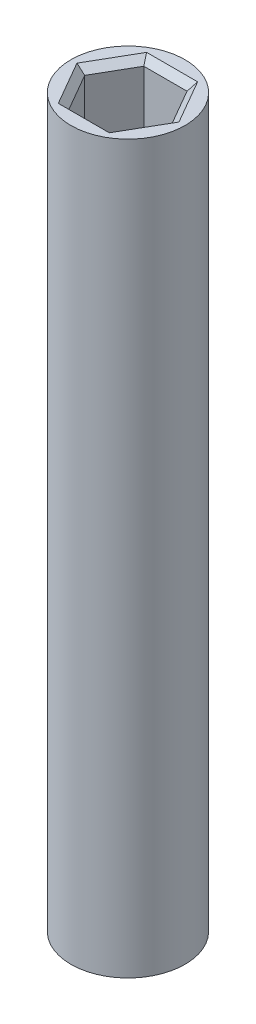
SolidWorks part; units mm, degrees
material "ABS"
ref_plane "Front Plane" through (0, 0, 0) normal (0, 0, 1) x (1, 0, 0)
ref_plane "Top Plane" through (0, 0, 0) normal (0, 1, 0) x (1, 0, 0)
ref_plane "Right Plane" through (0, 0, 0) normal (1, 0, 0) x (0, 0, -1)
sketch "Sketch1" plane through (0, 0, 0) normal (0, 1, 0) x (1, 0, 0)
  circle A0 centre (0, 0) radius 4.25
  dimension "D1" = 8.5
extrude "Boss-Extrude1" add sketch "Sketch1" along normal blind 54.1152
sketch "Sketch2" plane through (0, 54.1152, 0) normal (0, 1, 0) x (1, 0, 0)
  line L0 (0, 2.79) -> (0, -2.79)
  line L1 (1.6108, 2.79) -> (-1.6108, 2.79)
  line L2 (-1.6108, 2.79) -> (-3.2216, 0)
  line L3 (-3.2216, 0) -> (-1.6108, -2.79)
  line L4 (-1.6108, -2.79) -> (1.6108, -2.79)
  line L5 (1.6108, -2.79) -> (3.2216, 0)
  line L6 (3.2216, 0) -> (1.6108, 2.79)
  line L7 (0, 4.25) -> (0, -4.25) construction
  circle A0 centre (0, 0) radius 2.79 construction
  circle A1 centre (0, 0) radius 4.25 construction
  dimension "D1" = 5.58
extrude "Cut-Extrude1" cut sketch "Sketch2" against normal blind 6.6 contours L3 L4 L0 L1 L2 | L5 L6 L1 L0 L4
chamfer "Chamfer1" distance 0.5 angle 45 6 edges at (0, 54.1152, 2.79) (2.4162, 54.1152, 1.395) (2.4162, 54.1152, -1.395) (0, 54.1152, -2.79) (-2.4162, 54.1152, 1.395) (-2.4162, 54.1152, -1.395)
sketch "Sketch3" plane through (0, 0, 0) normal (0, -1, 0) x (1, 0, 0)
  line L0 (0, 4.25) -> (0, -4.25) construction
  line L1 (-1.3615, 2.9198) -> (-3.2094, 0.2808)
  line L2 (-3.2094, 0.2808) -> (-1.8478, -2.639)
  line L3 (-1.8478, -2.639) -> (1.3615, -2.9198)
  line L4 (1.3615, -2.9198) -> (3.2094, -0.2808)
  line L5 (3.2094, -0.2808) -> (1.8478, 2.639)
  line L6 (1.8478, 2.639) -> (-1.3615, 2.9198)
  line L7 (-1.3615, 2.9198) -> (1.3615, -2.9198)
  circle A0 centre (0, 0) radius 2.79 construction
  circle A1 centre (0, 0) radius 4.25 construction
  dimension "D1" = 5.58
  dimension "D2" = 25
extrude "Cut-Extrude2" cut sketch "Sketch3" against normal blind 6.6 contours L7 L1 L2 L3 | L6 L7 L4 L5
chamfer "Chamfer2" distance 0.5 angle 45 6 edges at (0.2432, 0, 2.7794) (-2.2854, 0, 1.6003) (-2.5286, 0, -1.1791) (-0.2432, 0, -2.7794) (2.2854, 0, -1.6003) (2.5286, 0, 1.1791)
sketch3d "3DSketch1"
  line L0 (0, 0, 0) -> (0, 54.1152, 0)
